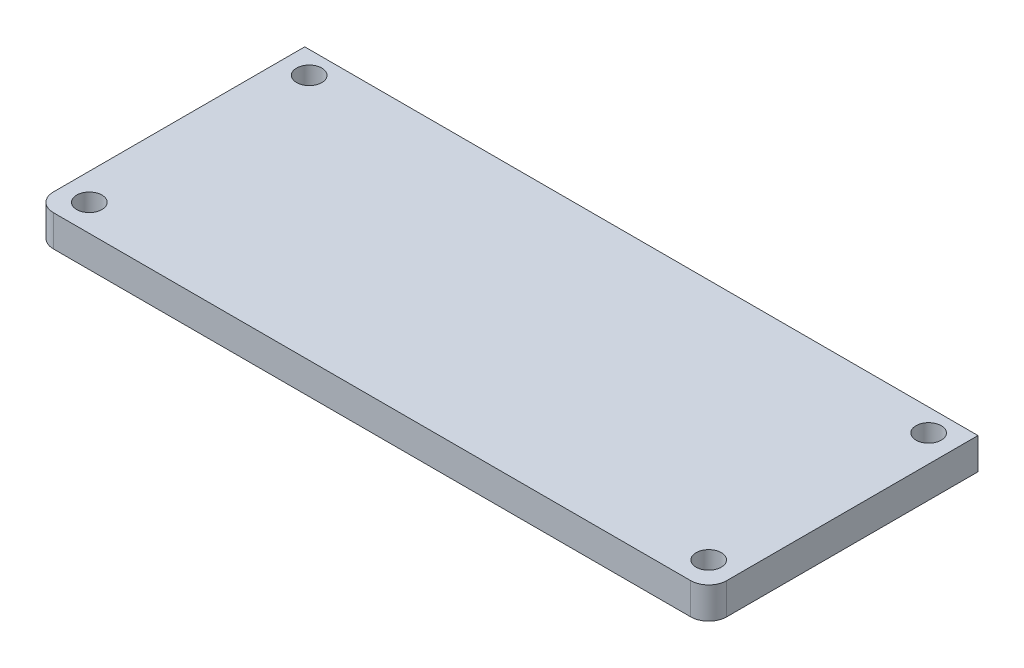
SolidWorks part; units mm, degrees
material "6061-T6 Al"
ref_plane "Front" through (0, 0, 0) normal (0, 0, 1) x (1, 0, 0)
ref_plane "Top" through (0, 0, 0) normal (0, 1, 0) x (1, 0, 0)
ref_plane "Right" through (0, 0, 0) normal (1, 0, 0) x (0, 0, -1)
sketch "Sketch1" plane through (0, 0, 0) normal (0, 1, 0) x (1, 0, 0)
  line L1 (95.25, -38.1) -> (-95.25, -38.1)
  line L2 (95.25, -38.1) -> (95.25, 38.1)
  line L3 (95.25, 38.1) -> (-95.25, 38.1)
  line L4 (-95.25, -38.1) -> (-95.25, 38.1)
  line L5 (95.25, -38.1) -> (-95.25, 38.1) construction
  line L6 (95.25, 38.1) -> (-95.25, -38.1) construction
  point P0 (0, 0)
  dimension "D1" = 190.5
  dimension "D2" = 76.2
extrude "Boss-Extrude1" add sketch "Sketch1" along normal blind 8.89
hole_wizard "1/4 Clearance Hole1" positions "Sketch3" profile "Sketch2" hole size "1/4" standard "Ansi Inch" end condition up to next
sketch "Sketch3" plane through (0, 8.89, 0) normal (0, 1, 0) x (-1, 0, 0)
  line L0 (95.25, -38.1) -> (95.25, 38.1) construction
  line L2 (-95.25, 38.1) -> (-95.25, -38.1) construction
  line L3 (95.25, 38.1) -> (-95.25, 38.1) construction
  point P0 (87.63, -31.75)
  point P1 (-87.63, -31.75)
  point P3 (-87.63, 30.48)
  point P5 (87.63, 30.48)
  dimension "D1" = 7.62
  dimension "D2" = 62.23
  dimension "D3" = 7.62
  dimension "D4" = 62.23
  dimension "D5" = 7.62
  dimension "D6" = 7.62
  dimension "D7" = 7.62
  dimension "D8" = 7.62
sketch "Sketch2" plane through (-87.63, 8.89, -31.75) normal (1, 0, 0) x (0, 0, 1)
  line L0 (0, 0) -> (0, 8.89)
  line L1 (0, 8.89) -> (3.5712, 8.89)
  line L2 (3.5712, 8.89) -> (3.5712, 0)
  line L5 (3.5712, 0) -> (0, 0)
  line L11 (0, -6.35) -> (0, 107.95) construction
  dimension "Thru Hole Dia." = 7.1425
  dimension "Thru Hole Depth" = 8.89
fillet "Fillet1" radius 5.08 2 edges at (95.25, 4.445, 38.1) (-95.25, 4.445, 38.1)
